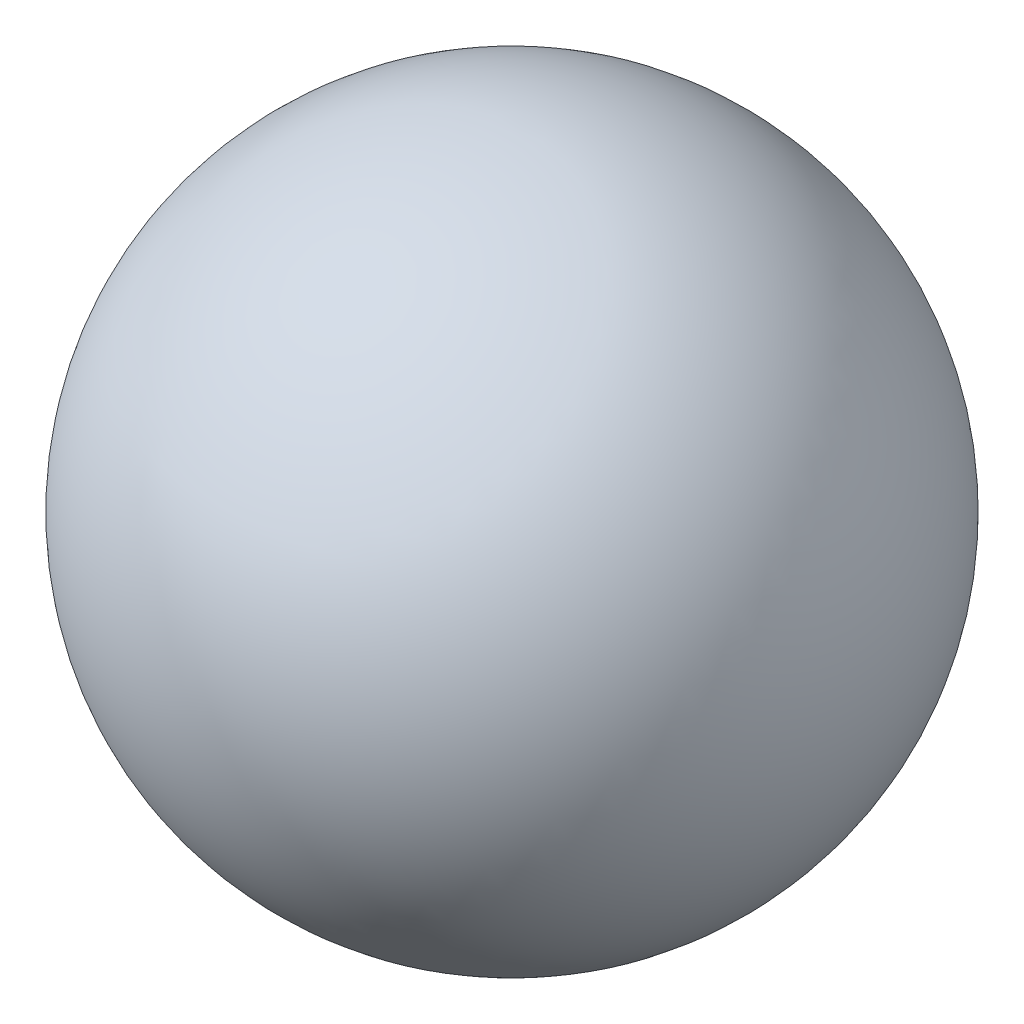
SolidWorks part; units mm, degrees
ref_plane "Front Plane" through (0, 0, 0) normal (0, 0, 1) x (1, 0, 0)
ref_plane "Top Plane" through (0, 0, 0) normal (0, 1, 0) x (1, 0, 0)
ref_plane "Right Plane" through (0, 0, 0) normal (1, 0, 0) x (0, 0, -1)
sketch "Sketch1" plane through (0, 0, 0) normal (0, 0, 1) x (1, 0, 0)
  line L0 (0, 0) -> (0, 330.2) construction
  line L1 (0, 330.2) -> (0, 0)
  arc A0 (0, 330.2) -> (0, 0) centre (0, 165.1) cw
  dimension "D1" = 330.2
revolve "Revolve1" add sketch "Sketch1" angle 360 about L0
